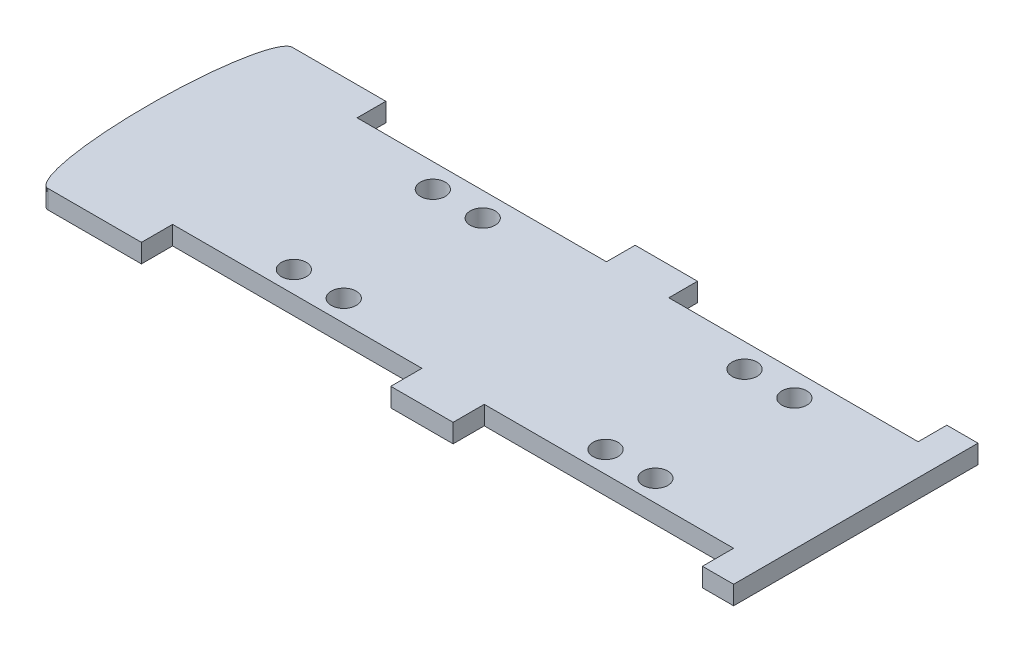
SolidWorks part; units mm, degrees
material "AISI 316 退火不锈钢条 (SS)"
ref_plane "前视基准面" through (0, 0, 0) normal (0, 0, 1) x (1, 0, 0)
ref_plane "上视基准面" through (0, 0, 0) normal (0, 1, 0) x (1, 0, 0)
ref_plane "右视基准面" through (0, 0, 0) normal (1, 0, 0) x (0, 0, -1)
sketch "草图1" plane through (0, 0, 0) normal (0, 1, 0) x (1, 0, 0)
  line L0 (-550, -196.0238) -> (-400, -196.0238)
  line L1 (-550, 196.0238) -> (550, 196.0238)
  line L2 (-550, 196.0238) -> (-550, -196.0238)
  line L3 (-550, -196.0238) -> (550, -196.0238)
  line L4 (550, 196.0238) -> (550, -196.0238)
  line L7 (550, -196.0238) -> (500, -196.0238)
  line L9 (-550, 196.0238) -> (-357.0577, 196.0238)
  line L11 (-400, -196.0238) -> (0, -196.0238)
  line L12 (-400, -196.0238) -> (-400, -146.0238)
  line L13 (-400, -146.0238) -> (0, -146.0238)
  line L14 (0, -196.0238) -> (0, -146.0238)
  line L15 (500, -196.0238) -> (100, -196.0238)
  line L16 (500, -196.0238) -> (500, -146.0238)
  line L17 (500, -146.0238) -> (100, -146.0238)
  line L18 (100, -196.0238) -> (100, -146.0238)
  line L19 (500, 200) -> (500, 150)
  line L20 (500, 150) -> (100, 150)
  line L21 (100, 200) -> (100, 150)
  line L22 (0, 200) -> (0, 150)
  line L23 (-400, 200) -> (-400, 150)
  line L24 (-400, 150) -> (0, 150)
  circle A0 centre (-160, -111.4627) radius 20
  circle A1 centre (-240, -111.4627) radius 20
  circle A2 centre (260, -111.4627) radius 20
  circle A3 centre (340, -111.4627) radius 20
  circle A4 centre (340, 111.4627) radius 20
  circle A5 centre (260, 111.4627) radius 20
  circle A6 centre (-160, 111.4627) radius 20
  circle A7 centre (-240, 111.4627) radius 20
  ellipse E0 centre (-550, 0) end of major axis (-550, -196.0238) minor radius 35
  point P0 (0, 0)
  dimension "D1" = 70
extrude "凸台-拉伸2" add sketch "草图1" along normal blind 30 contours E0 L0 L12 L13 L14 L3 L18 L17 L16 L4 L1 L19 L20 L21 L22 L24 L23 A7 A4 A3 A1 A0 A2 A5 A6 | L2 E0 | L2 E0
